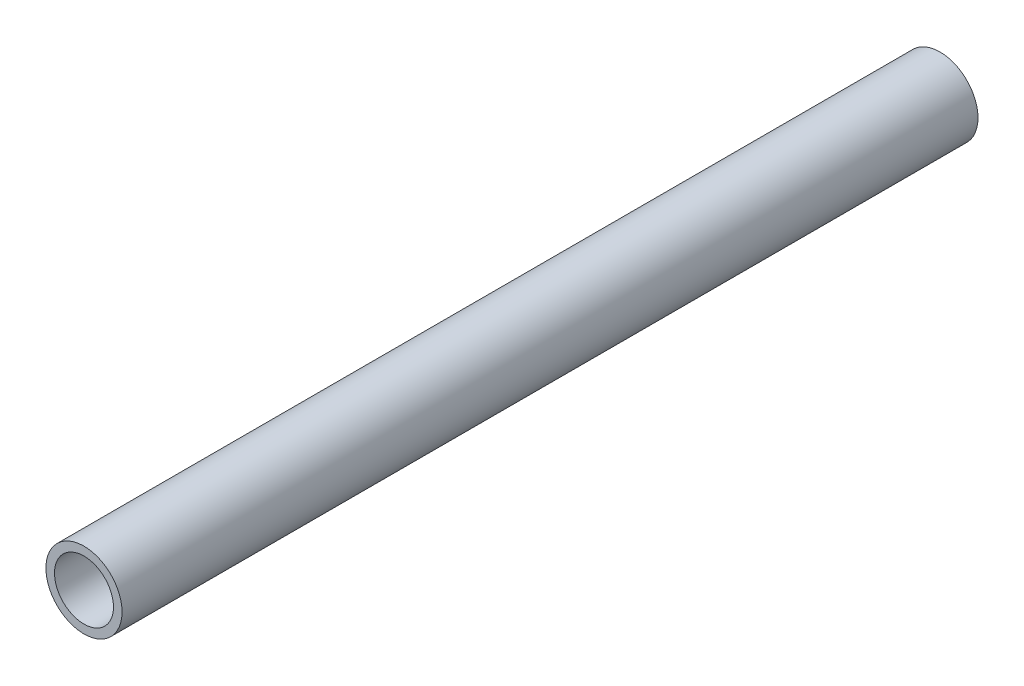
SolidWorks part; units mm, degrees
ref_plane "Front Plane" through (0, 0, 0) normal (0, 0, 1) x (1, 0, 0)
ref_plane "Top Plane" through (0, 0, 0) normal (0, 1, 0) x (1, 0, 0)
ref_plane "Right Plane" through (0, 0, 0) normal (1, 0, 0) x (0, 0, -1)
sketch "Sketch1" plane through (0, 0, 0) normal (0, 0, 1) x (1, 0, 0)
  circle A0 centre (0, 0) radius 10.335
  circle A1 centre (0, 0) radius 13.335
  dimension "D1" = 26.67
  dimension "D2" = 3
extrude "Boss-Extrude1" add sketch "Sketch1" along normal mid plane 300
